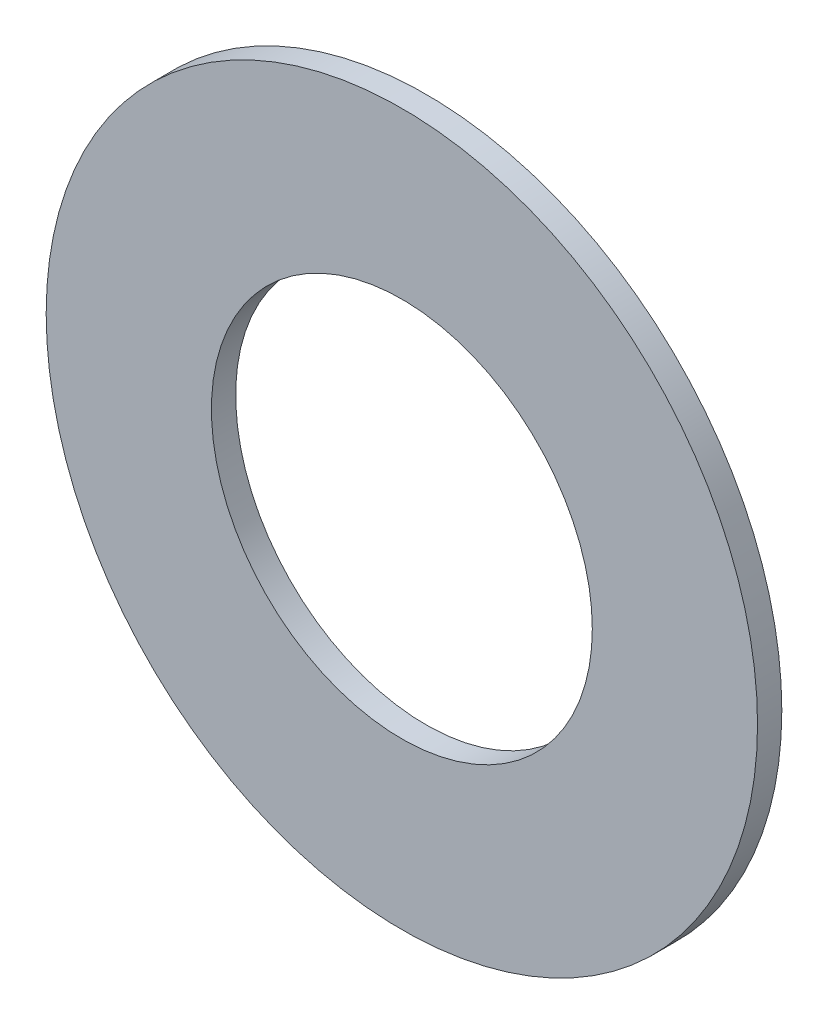
SolidWorks part; units mm, degrees
ref_plane "Front Plane" through (0, 0, 0) normal (0, 0, 1) x (1, 0, 0)
ref_plane "Top Plane" through (0, 0, 0) normal (0, 1, 0) x (1, 0, 0)
ref_plane "Right Plane" through (0, 0, 0) normal (1, 0, 0) x (0, 0, -1)
sketch "Sketch1" plane through (0, 0, 0) normal (0, 0, 1) x (1, 0, 0)
  line L0 (-6.35, 0) -> (6.35, 0) construction
  circle A0 centre (0, 0) radius 11.9062 construction
  circle A1 centre (0, 0) radius 6.3754 construction
  dimension "OD" = 23.8125
  dimension "ID" = 12.7508
  dimension "For Shaft Diameter" = 12.7
sketch "Sketch2" plane through (0, 0, 0) normal (1, 0, 0) x (0, 0, -1)
  line L4 (0.4064, 11.9062) -> (-0.4064, 11.9062) construction
  point P0 (0, 11.9062)
  dimension "Thickness" = 0.8128
sketch "Sketch3" plane through (0, 0, 0) normal (0, 0, 1) x (1, 0, 0)
  circle A0 centre (0, 0) radius 6.3754 construction
  circle A1 centre (0, 0) radius 11.9062 construction
  circle A3 centre (0, 0) radius 6.3754
  circle A5 centre (0, 0) radius 11.9062
extrude "Boss-Extrude1" add sketch "Sketch3" against normal up to vertex (0.4064 mm away) and the other way up to vertex (0.4064 mm away)
equation "\"D1\"= \"Thickness@Sketch2\""
